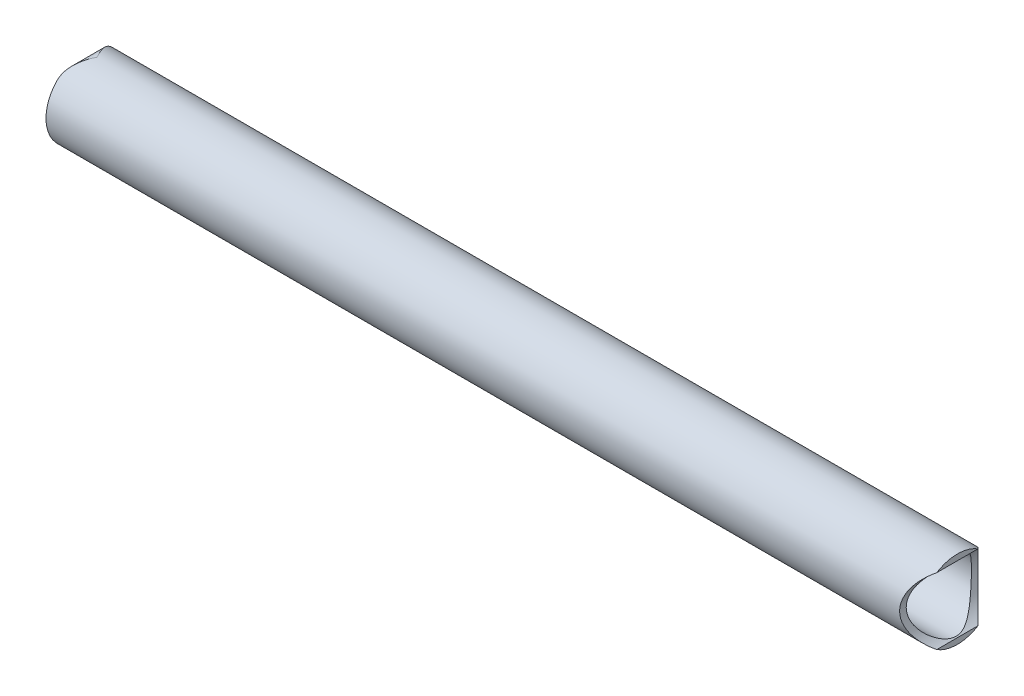
SolidWorks part; units mm, degrees
material "6061-T6 (SS)"
ref_plane "Front Plane" through (0, 0, 0) normal (0, 0, 1) x (1, 0, 0)
ref_plane "Top Plane" through (0, 0, 0) normal (0, 1, 0) x (1, 0, 0)
ref_plane "Right Plane" through (0, 0, 0) normal (1, 0, 0) x (0, 0, -1)
sketch "Sketch1" plane through (0, 0, 0) normal (1, 0, 0) x (0, 0, -1)
  circle A0 centre (0, 0) radius 21.082
  circle A1 centre (0, 0) radius 17.526
  dimension "D1" = 42.164
  dimension "D2" = 35.052
extrude "Boss-Extrude1" add sketch "Sketch1" along normal blind 469.1062
sketch "Sketch2" plane through (0, 0, 0) normal (0, 0, 1) x (1, 0, 0)
  line L0 (0, 21.082) -> (0, 14.732)
  line L1 (0, 21.082) -> (0, -21.082) construction
  line L2 (0, 21.082) -> (6.35, 21.082)
  line L3 (469.1062, 21.082) -> (0, 21.082) construction
  arc A0 (6.35, 21.082) -> (0, 14.732) centre (6.35, 14.732) ccw
  dimension "D1" = 6.35
extrude "Cut-Extrude1" cut sketch "Sketch2" against normal through all both and the other way through all
sketch "Sketch3" plane through (0, 0, 0) normal (0, 0, 1) x (1, 0, 0)
  line L0 (0, 14.732) -> (0, -21.082) construction
  circle A0 centre (480.2188, 0) radius 21.082
  dimension "D1" = 42.164
  dimension "D2" = 480.2188
extrude "Cut-Extrude2" cut sketch "Sketch3" against normal through all both and the other way through all
